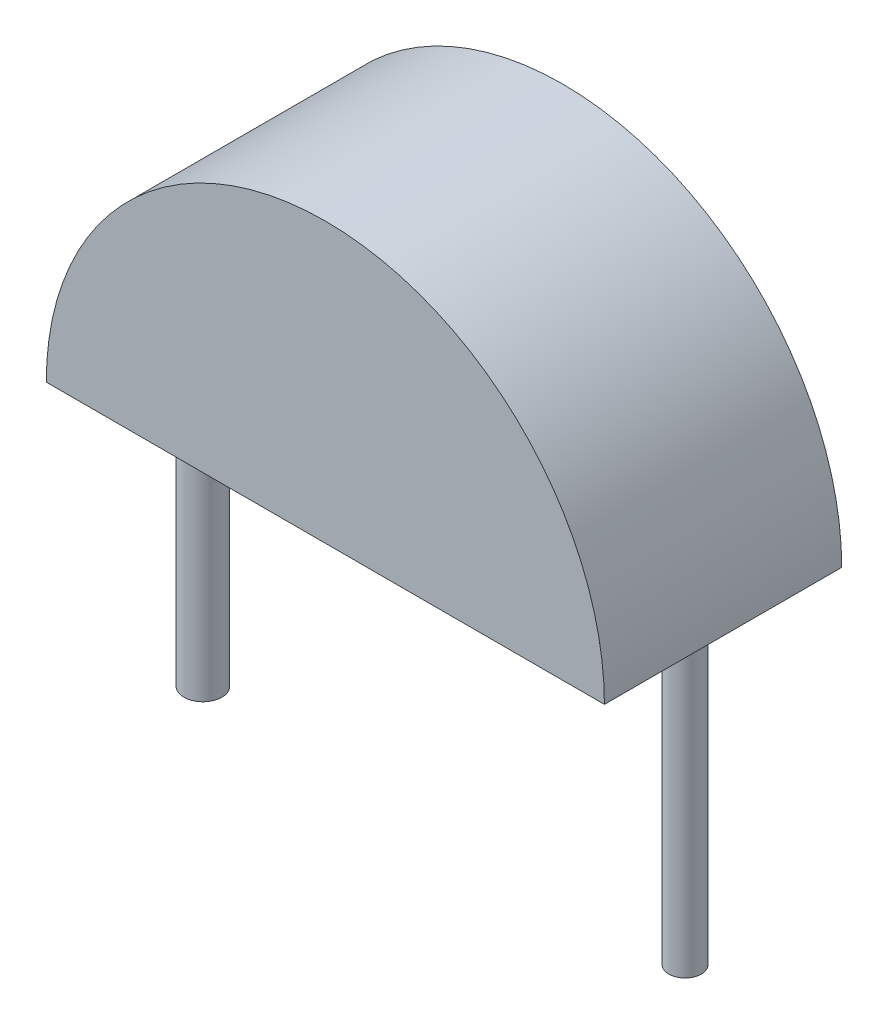
SolidWorks part; units mm, degrees
ref_plane "Front Plane" through (0, 0, 0) normal (0, 0, 1) x (1, 0, 0)
ref_plane "Top Plane" through (0, 0, 0) normal (0, 1, 0) x (1, 0, 0)
ref_plane "Right Plane" through (0, 0, 0) normal (1, 0, 0) x (0, 0, -1)
sketch "Sketch1" plane through (0, 0, 0) normal (0, 0, 1) x (1, 0, 0)
  line L0 (-2.94, 0) -> (2.94, 0)
  arc A0 (2.94, 0) -> (-2.94, 0) centre (0, 0) ccw
  dimension "D1" = 5.88
extrude "Boss-Extrude1" add sketch "Sketch1" along normal blind 2.5
sketch "Sketch2" plane through (0, 0, 0) normal (0, -1, 0) x (1, 0, 0)
  line L0 (-2.94, 2.5) -> (-2.94, 0) construction
  line L1 (-2.94, 2.5) -> (2.94, 2.5) construction
  circle A0 centre (-2.54, 1.25) radius 0.2
  circle A1 centre (2.54, 1.25) radius 0.1716
  point P4 (-2.94, 1.25)
  point P9 (0, 2.5)
  dimension "D1" = 0.4
  dimension "D2" = 5.08
  dimension "D3" = 2.54
extrude "Boss-Extrude2" add sketch "Sketch2" along normal blind 3.2
equation "\"D2@Sketch2\"=2.54*2"
equation "\"D3@Sketch2\"=\"D2@Sketch2\"/2"
